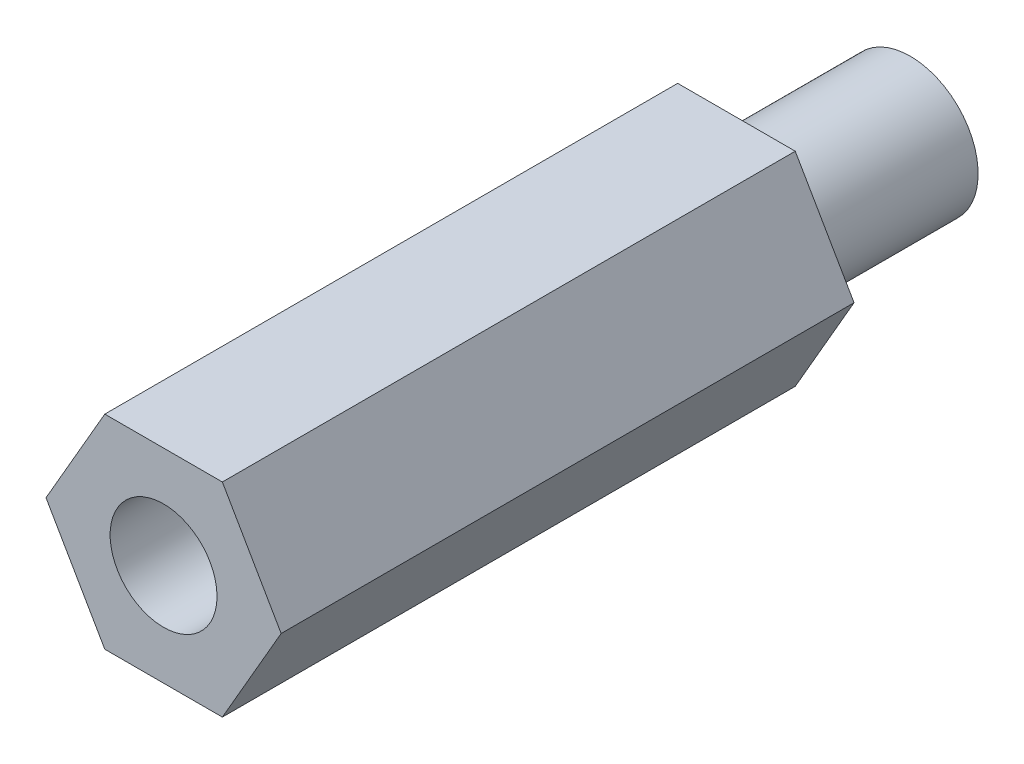
SolidWorks part; units mm, degrees
ref_plane "Front Plane" through (0, 0, 0) normal (0, 0, 1) x (1, 0, 0)
ref_plane "Top Plane" through (0, 0, 0) normal (0, 1, 0) x (1, 0, 0)
ref_plane "Right Plane" through (0, 0, 0) normal (1, 0, 0) x (0, 0, -1)
sketch "Sketch1" plane through (0, 0, 0) normal (0, 0, 1) x (1, 0, 0)
  line L1 (2.7496, -4.7625) -> (5.4993, 0)
  line L2 (5.4993, 0) -> (2.7496, 4.7625)
  line L3 (2.7496, 4.7625) -> (-2.7496, 4.7625)
  line L4 (-2.7496, 4.7625) -> (-5.4993, 0)
  line L5 (-5.4993, 0) -> (-2.7496, -4.7625)
  line L6 (-2.7496, -4.7625) -> (2.7496, -4.7625)
  circle A0 centre (0, 0) radius 4.7625 construction
  dimension "D1" = 9.525
extrude "Boss-Extrude1" add sketch "Sketch1" along normal blind 34.925
sketch "Sketch2" plane through (0, 0, 34.925) normal (0, 0, 1) x (1, 0, 0)
  circle A0 centre (0, 0) radius 2.5
  dimension "D1" = 5
extrude "Cut-Extrude1" cut sketch "Sketch2" against normal blind 9.525
sketch "Sketch4" plane through (0, 0, 0) normal (0, 0, -1) x (-1, 0, 0)
  circle A0 centre (0, 0) radius 3.175
  dimension "D1" = 6.35
extrude "Cut-Extrude2" cut sketch "Sketch4" against normal blind 8.128 flip side to cut
